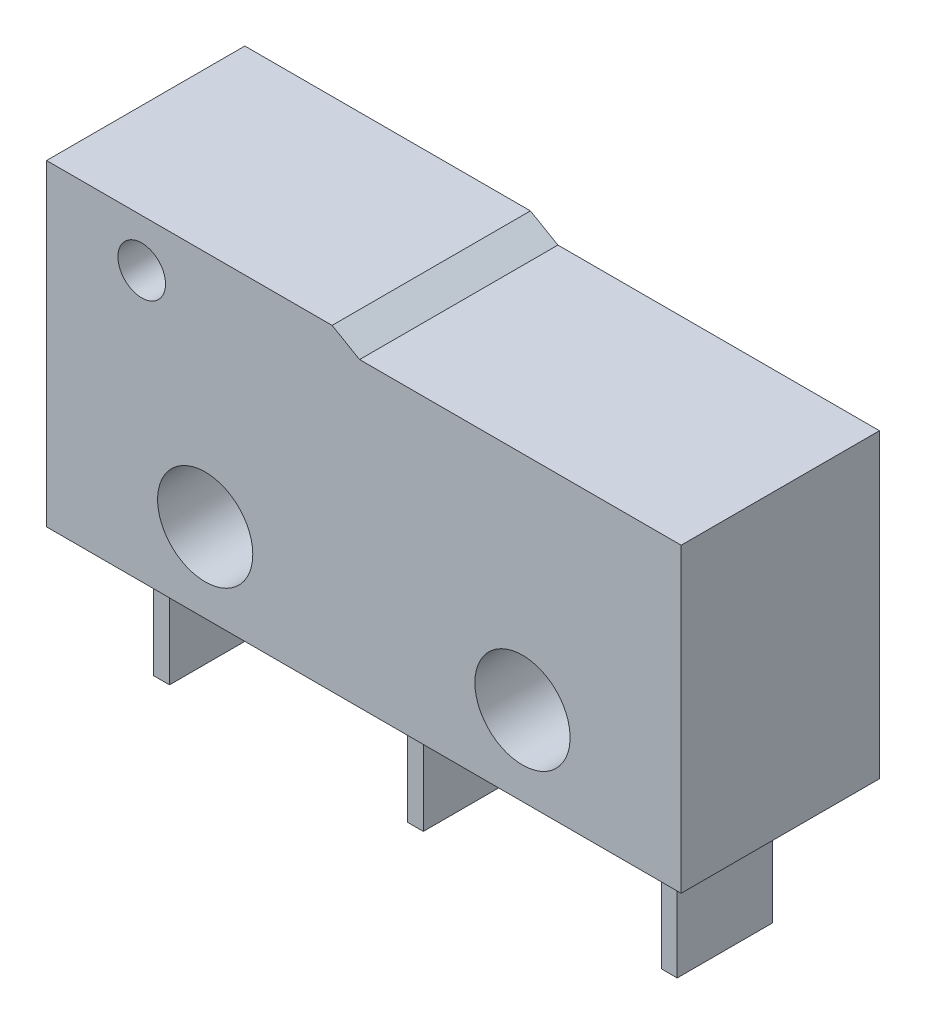
SolidWorks part; units mm, degrees
ref_plane "Front Plane" through (0, 0, 0) normal (0, 0, 1) x (1, 0, 0)
ref_plane "Top Plane" through (0, 0, 0) normal (0, 1, 0) x (1, 0, 0)
ref_plane "Right Plane" through (0, 0, 0) normal (1, 0, 0) x (0, 0, -1)
sketch "Sketch1" plane through (0, 0, 0) normal (0, 0, 1) x (1, 0, 0)
  line L0 (10, 0) -> (-10, 0)
  line L1 (-10, 0) -> (-10, 10)
  line L2 (-10, 10) -> (-1, 10)
  line L3 (-1, 10) -> (-0.134, 9.5)
  line L4 (-0.134, 9.5) -> (10, 9.5)
  line L5 (10, 9.5) -> (10, 0)
  line L6 (0, 0) -> (0, 13.8279) construction
  circle A0 centre (-5, 2.5) radius 1.5
  circle A1 centre (5, 2.5) radius 1.5
  circle A2 centre (-7, 8.5) radius 0.75
  point P4 (0, 0)
  dimension "D8" = 3
  dimension "D11" = 1.5
  dimension "D1" = 20
  dimension "D2" = 10
  dimension "D3" = 9.5
  dimension "D4" = 9
  dimension "D5" = 30
  dimension "D6" = 5
  dimension "D7" = 2.5
  dimension "D9" = 3
  dimension "D10" = 1.5
extrude "Boss-Extrude1" add sketch "Sketch1" along normal mid plane 6.25
sketch "Sketch2" plane through (0, 0, 0) normal (0, -1, 0) x (1, 0, 0)
  line L0 (-10, 3.125) -> (-10, -3.125) construction
  line L1 (0.25, -1.5) -> (-0.25, -1.5)
  line L2 (0.25, -1.5) -> (0.25, 1.5)
  line L3 (0.25, 1.5) -> (-0.25, 1.5)
  line L4 (-0.25, -1.5) -> (-0.25, 1.5)
  line L5 (0.25, -1.5) -> (-0.25, 1.5) construction
  line L6 (0.25, 1.5) -> (-0.25, -1.5) construction
  line L7 (-7.75, -1.5) -> (-8.25, -1.5)
  line L8 (-7.75, -1.5) -> (-7.75, 1.5)
  line L9 (-7.75, 1.5) -> (-8.25, 1.5)
  line L10 (-8.25, -1.5) -> (-8.25, 1.5)
  line L11 (-7.75, -1.5) -> (-8.25, 1.5) construction
  line L12 (-7.75, 1.5) -> (-8.25, -1.5) construction
  line L13 (0, 0) -> (0, 3.408) construction
  line L14 (7.75, 1.5) -> (8.25, 1.5)
  line L15 (8.25, -1.5) -> (8.25, 1.5)
  line L16 (7.75, -1.5) -> (8.25, -1.5)
  line L17 (7.75, -1.5) -> (7.75, 1.5)
  point P0 (0, 0)
  point P6 (-8, 0)
  dimension "D1" = 0.5
  dimension "D2" = 3
  dimension "D3" = 2
extrude "Boss-Extrude2" add sketch "Sketch2" along normal blind 4
sketch "Sketch3" plane through (0, 0, -3.125) normal (0, 0, -1) x (-1, 0, 0)
  line L0 (-14.5495, 18) -> (12.6167, 18)
  line L1 (10, 0) -> (-10, 0) construction
  dimension "D1" = 18
